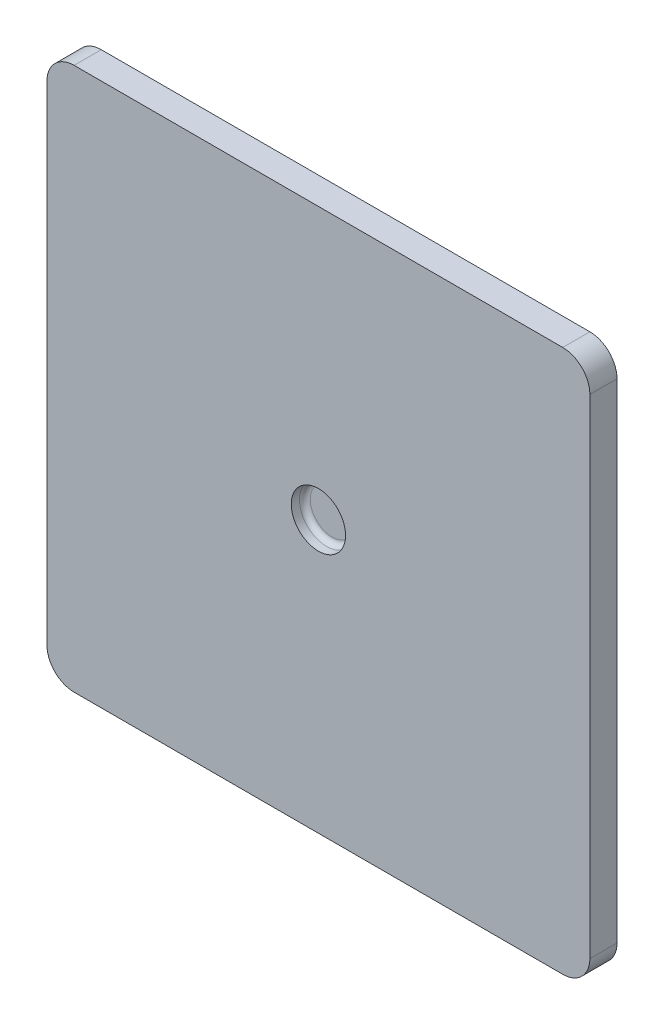
SolidWorks part; units mm, degrees
material "Oak"
ref_plane "Front Plane" through (0, 0, 0) normal (0, 0, 1) x (1, 0, 0)
ref_plane "Top Plane" through (0, 0, 0) normal (0, 1, 0) x (1, 0, 0)
ref_plane "Right Plane" through (0, 0, 0) normal (1, 0, 0) x (0, 0, -1)
sketch "Sketch1" plane through (0, 0, 0) normal (0, 0, 1) x (1, 0, 0)
  line L1 (-90, -100) -> (90, -100)
  line L2 (-100, -90) -> (-100, 90)
  line L3 (-90, 100) -> (90, 100)
  line L4 (100, -90) -> (100, 90)
  line L5 (-100, -100) -> (100, 100) construction
  line L6 (-100, 100) -> (100, -100) construction
  arc A0 (-100, 90) -> (-90, 100) centre (-90, 90) cw
  arc A1 (-90, -100) -> (-100, -90) centre (-90, -90) cw
  arc A2 (90, -100) -> (100, -90) centre (90, -90) ccw
  arc A3 (100, 90) -> (90, 100) centre (90, 90) ccw
  point P0 (0, 0)
  dimension "D1" = 10
extrude "Boss-Extrude1" add sketch "Sketch1" along normal blind 10
sketch "Sketch2" plane through (0, 0, 10) normal (0, 0, 1) x (1, 0, 0)
  circle A0 centre (0, 0) radius 10
extrude "Cut-Extrude2" cut sketch "Sketch2" against normal blind 5
fillet "Fillet1" radius 2 1 edges at (10, 0, 5)
